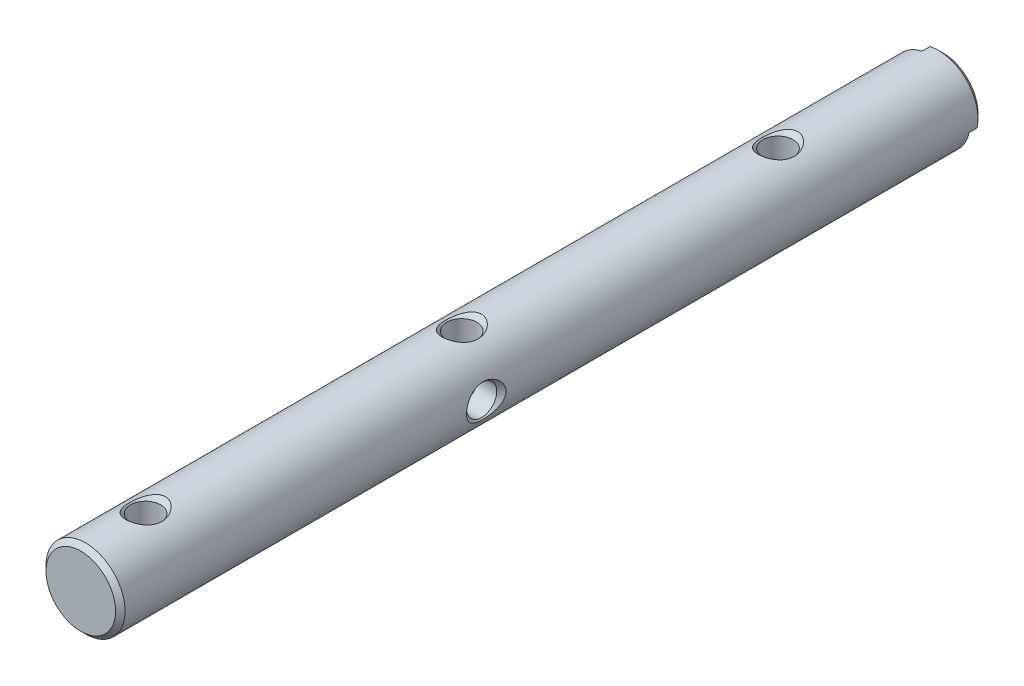
SolidWorks part; units mm, degrees
material "304 SSTL"
ref_plane "Front" through (0, 0, 0) normal (0, 0, 1) x (1, 0, 0)
ref_plane "Top" through (0, 0, 0) normal (0, 1, 0) x (1, 0, 0)
ref_plane "Right" through (0, 0, 0) normal (1, 0, 0) x (0, 0, -1)
sketch "Sketch1" plane through (0, 0, 0) normal (0, 0, 1) x (1, 0, 0)
  circle A0 centre (0, 0) radius 6.35
  dimension "D1" = 12.7
extrude "Boss-Extrude1" add sketch "Sketch1" along normal blind 136.525
chamfer "Chamfer1" distance 0.762 angle 45 1 edges at (6.35, 0, 136.525)
ref_plane "Plane1" through (0, 6.35, 0) normal (0, 1, 0) x (-1, 0, 0)
hole_wizard "#11 (0.191) Diameter Hole1" positions "Sketch3" profile "Sketch2" hole size "#11" standard "Ansi Inch"
sketch "Sketch3" plane through (0, 6.35, 0) normal (0, 1, 0) x (-1, 0, 0)
  line L0 (0, 136.525) -> (0, 126.111) construction
  line L1 (5.588, 136.525) -> (-5.588, 136.525) construction
  line L2 (0, 126.111) -> (0, 75.311) construction
  line L3 (0, 75.311) -> (0, 24.511) construction
  point P0 (0, 24.511)
  point P1 (0, 75.311)
  point P3 (0, 126.111)
  dimension "D1" = 50.8
  dimension "D2" = 10.414
sketch "Sketch2" plane through (0, 6.35, 24.511) normal (1, 0, 0) x (0, 0, 1)
  line L0 (0, 0) -> (0, 14.1575)
  line L1 (0, 14.1575) -> (2.4257, 12.7)
  line L2 (2.4257, 12.7) -> (2.4257, 0.7493)
  line L3 (2.4257, 0.7493) -> (3.175, 0)
  line L5 (3.175, 0) -> (0, 0)
  line L6 (-2.4257, 0.7493) -> (-3.175, 0) construction
  line L10 (0, 14.1575) -> (-2.4257, 12.7) construction
  line L11 (0, -6.35) -> (0, 107.95) construction
  dimension "Hole Dia." = 4.8514
  dimension "Hole Depth" = 12.7
  dimension "Near C'Sink Dia." = 6.35
  dimension "Near C'Sink Angle" = 90
  dimension "Drill Angle" = 118
hole_wizard "#8-32 Tapped Hole1" positions "Sketch5" profile "Sketch4" tap size "#8-32" standard "Ansi Inch"
sketch "Sketch5" plane through (0, 0, 0) normal (0, 0, -1) x (-1, 0, 0)
  point P0 (0, 0)
sketch "Sketch4" plane through (0, 0, 0) normal (1, 0, 0) x (0, 1, 0)
  line L0 (0, 0) -> (0, 11.7566)
  line L1 (0, 11.7566) -> (1.7272, 10.7188)
  line L2 (1.7272, 10.7188) -> (1.7272, 0)
  line L5 (1.7272, 0) -> (0, 0)
  line L10 (0, 11.7566) -> (-1.7272, 10.7188) construction
  line L11 (0, -6.35) -> (0, 107.95) construction
  dimension "Tap Drill Dia." = 3.4544
  dimension "Tap Drill Depth" = 10.7188
  dimension "Drill Angle" = 118
cosmetic thread "Hole Thread2" parameters "D1"=8.3312, "D2"=4.1656
ref_plane "Plane2" through (6.35, 0, 0) normal (1, 0, 0) x (0, 0, -1)
hole_wizard "#11 (0.191) Diameter Hole2" positions "Sketch7" profile "Sketch6" hole size "#11" standard "Ansi Inch"
sketch "Sketch7" plane through (6.35, 0, 0) normal (1, 0, 0) x (0, 0, -1)
  line L0 (0, 0) -> (-77.724, 0) construction
  point P0 (-77.724, 0)
  dimension "D1" = 77.724
sketch "Sketch6" plane through (6.35, 0, 77.724) normal (0, 1, 0) x (0, 0, -1)
  line L0 (0, 0) -> (0, 14.1575)
  line L1 (0, 14.1575) -> (2.4257, 12.7)
  line L2 (2.4257, 12.7) -> (2.4257, 0.7493)
  line L3 (2.4257, 0.7493) -> (3.175, 0)
  line L5 (3.175, 0) -> (0, 0)
  line L6 (-2.4257, 0.7493) -> (-3.175, 0) construction
  line L10 (0, 14.1575) -> (-2.4257, 12.7) construction
  line L11 (0, -6.35) -> (0, 107.95) construction
  dimension "Hole Dia." = 4.8514
  dimension "Hole Depth" = 12.7
  dimension "Near C'Sink Dia." = 6.35
  dimension "Near C'Sink Angle" = 90
  dimension "Drill Angle" = 118
sketch "Sketch8" plane through (0, 0, 0) normal (0, 0, -1) x (-1, 0, 0)
  line L0 (-6.2039, -1.3545) -> (1.3545, 6.2039)
  line L1 (0, 0) -> (-2.4247, 2.4247) construction
  arc A0 (1.3545, 6.2039) -> (-6.2039, -1.3545) centre (0, 0) ccw
  circle A1 centre (0, 0) radius 6.35 construction
  circle A2 centre (0, 0) radius 1.7272 construction
  dimension "D1" = 3.429
extrude "Boss-Extrude2" add sketch "Sketch8" along normal blind 2.032
chamfer "Chamfer2" distance 0.762 angle 45 1 edges at (4.4901, 4.4901, -2.032)
ref_plane "Plane3" through (-6.35, 0, 0) normal (1, 0, 0) x (0, 0, -1)
ref_plane "Plane4" through (0, -6.35, 0) normal (0, 1, 0) x (-1, 0, 0)
sketch "Sketch9" plane through (-6.35, 0, 0) normal (1, 0, 0) x (0, 0, -1)
  circle A0 centre (-77.724, 0) radius 3.175
  dimension "D1" = 6.35
extrude "Cut-Extrude3" cut sketch "Sketch9" along normal blind 2.54 draft 45
sketch "Sketch10" plane through (0, -6.35, 0) normal (0, 1, 0) x (-1, 0, 0)
  circle A0 centre (0, 126.111) radius 3.175
  circle A1 centre (0, 75.311) radius 3.175
  circle A2 centre (0, 24.511) radius 3.175
  dimension "D1" = 6.35
extrude "Cut-Extrude5" cut sketch "Sketch10" along normal blind 2.54 draft 45
